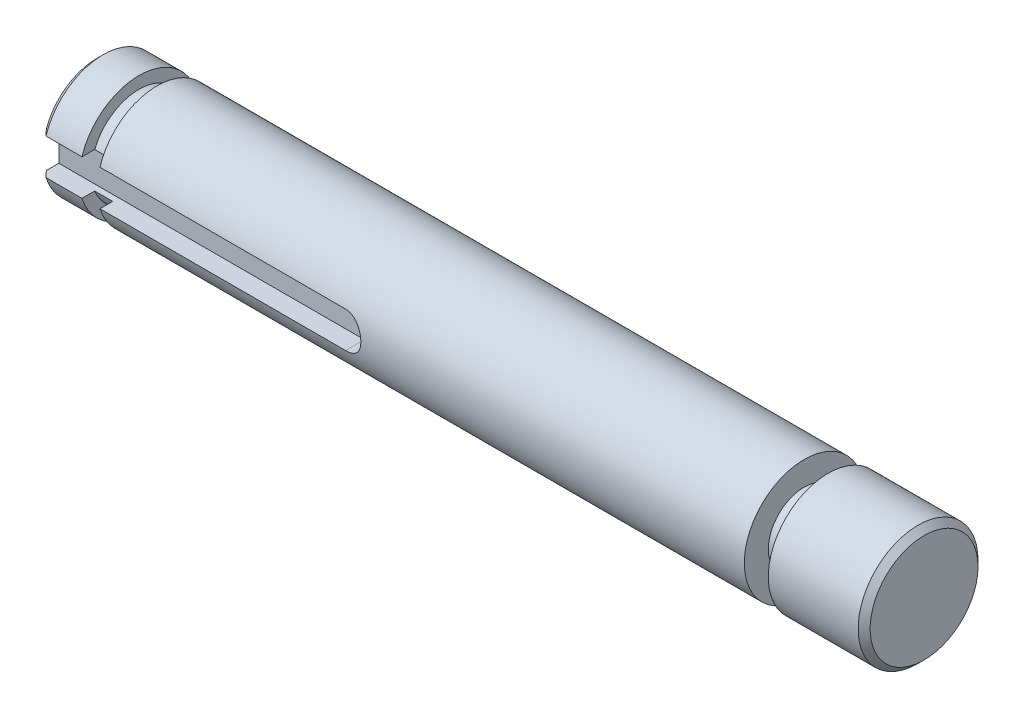
SolidWorks part; units mm, degrees
ref_plane "Front Plane" through (0, 0, 0) normal (0, 0, 1) x (1, 0, 0)
ref_plane "Top Plane" through (0, 0, 0) normal (0, 1, 0) x (1, 0, 0)
ref_plane "Right Plane" through (0, 0, 0) normal (1, 0, 0) x (0, 0, -1)
sketch "Sketch1" plane through (0, 0, 0) normal (1, 0, 0) x (0, 0, -1)
  circle A0 centre (0, 0) radius 5
  dimension "D1" = 10
extrude "Boss-Extrude1" add sketch "Sketch1" along normal mid plane 69
cosmetic thread "Cosmetic Thread1" parameters "D1"=7, "D2"=6.619
sketch "Sketch2" plane through (34.5, 0, 0) normal (1, 0, 0) x (0, 0, -1)
  circle A0 centre (0, 0) radius 3
  circle A1 centre (0, 0) radius 5
  circle A2 centre (0, 0) radius 5
  dimension "D2" = 6
  dimension "D1" = 0
extrude "Cut-Extrude1" cut sketch "Sketch2" along normal blind 2 from offset 10 offset against normal yes
sketch "Sketch3" plane through (-34.5, 0, 0) normal (-1, 0, 0) x (0, 0, 1)
  circle A0 centre (0, 0) radius 4
  circle A1 centre (0, 0) radius 5
  circle A2 centre (0, 0) radius 5
  dimension "D2" = 8
  dimension "D1" = 0
extrude "Cut-Extrude2" cut sketch "Sketch3" along normal blind 1.5 from offset 5 offset against normal yes
chamfer "Chamfer1" distance 0.5 angle 45 2 edges at (34.5, 0, -5) (-34.5, 0, -5)
sketch "Sketch4" plane through (0, 0, 0) normal (0, 0, 1) x (1, 0, 0)
  line L0 (-34.5, 0) -> (-9, 0) construction
  line L1 (-34.5, 4.5) -> (-34.5, -4.5) construction
  line L2 (-34.5, 1.5) -> (-9, 1.5)
  line L3 (-34.5, -1.5) -> (-9, -1.5)
  line L4 (-34.5, 1.5) -> (-34.5, -1.5)
  arc A1 (-9, -1.5) -> (-9, 1.5) centre (-9, 0) ccw
  point P5 (-21.7205, 0)
  point P10 (0, 0)
  dimension "D2" = 1.5
  dimension "D1" = 25.5
  dimension "D3" = 3
  dimension "D4" = 1.5
extrude "Cut-Extrude3" cut sketch "Sketch4" along normal through all from offset 3.2
